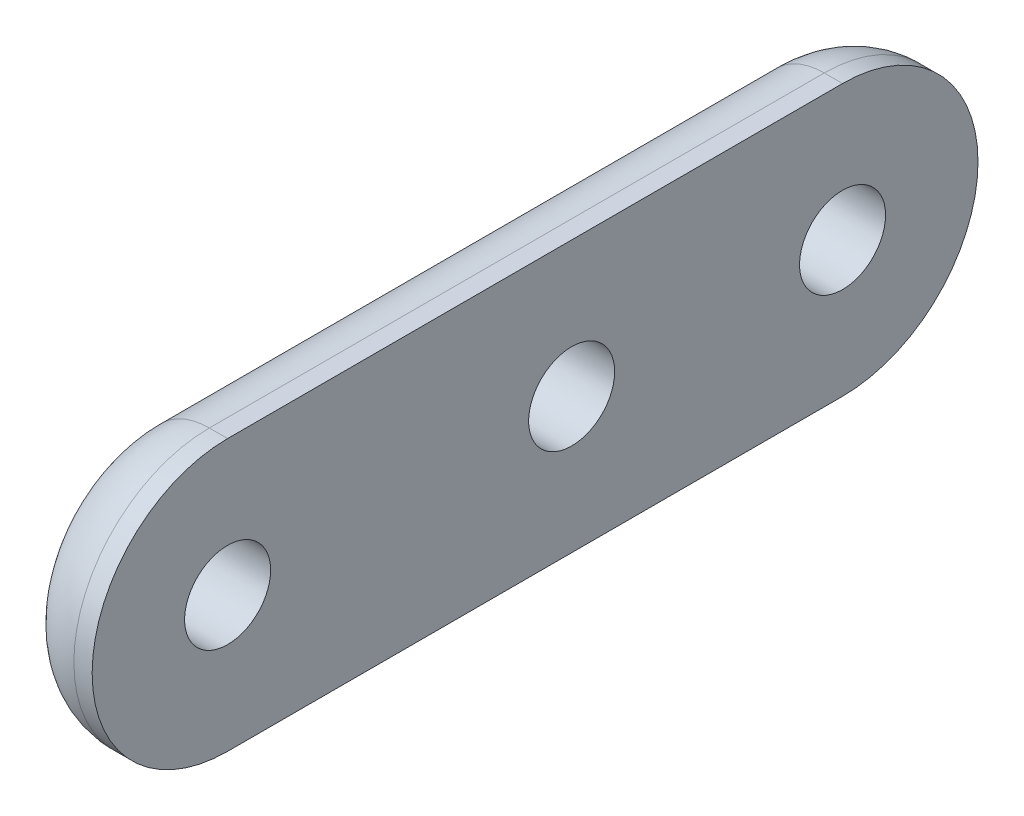
SolidWorks part; units mm, degrees
material "6061 Alloy"
ref_plane "Front Plane" through (0, 0, 0) normal (0, 0, 1) x (1, 0, 0)
ref_plane "Top Plane" through (0, 0, 0) normal (0, 1, 0) x (1, 0, 0)
ref_plane "Right Plane" through (0, 0, 0) normal (1, 0, 0) x (0, 0, -1)
sketch "Sketch2" plane through (0, 0, 0) normal (1, 0, 0) x (0, 0, -1)
  line L0 (-68.9265, 0) -> (71.4444, 0) construction
  line L1 (-58.1764, 10) -> (-12.7764, 10)
  line L2 (-58.1764, -10) -> (-12.7764, -10)
  circle A0 centre (-32.7764, 0) radius 3.175
  circle A1 centre (-12.7764, 0) radius 3.175
  circle A2 centre (-58.1764, 0) radius 3.175
  arc A3 (-12.7764, -10) -> (-12.7764, 10) centre (-12.7764, 0) ccw
  arc A4 (-58.1764, 10) -> (-58.1764, -10) centre (-58.1764, 0) ccw
  dimension "D1" = 6.35
  dimension "D2" = 6.35
  dimension "D4" = 6.35
  dimension "D3" = 20
  dimension "D5" = 25.4
extrude "Boss-Extrude1" add sketch "Sketch2" along normal blind 6.35
fillet "Fillet1" radius 5 4 edges at (0, 0, 2.7764) (0, -10, 35.4764) (0, 0, 68.1764) (0, 10, 35.4764)
